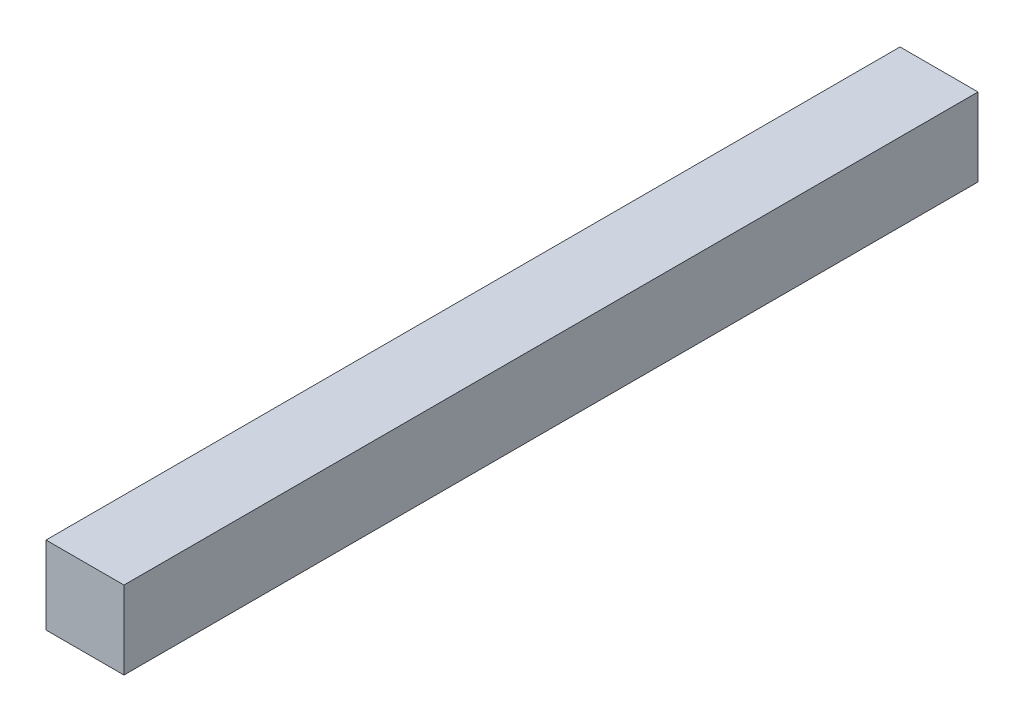
SolidWorks part; units mm, degrees
material "Pine"
ref_plane "Front Plane" through (0, 0, 0) normal (0, 0, 1) x (1, 0, 0)
ref_plane "Top Plane" through (0, 0, 0) normal (0, 1, 0) x (1, 0, 0)
ref_plane "Right Plane" through (0, 0, 0) normal (1, 0, 0) x (0, 0, -1)
sketch "Sketch1" plane through (0, 0, 0) normal (0, 0, 1) x (1, 0, 0)
  line L0 (21, 21) -> (-21, 21)
  line L1 (20, -20) -> (-20, -20)
  line L2 (20, -20) -> (20, 20)
  line L3 (20, 20) -> (-20, 20)
  line L4 (-20, -20) -> (-20, 20)
  line L5 (20, -20) -> (-20, 20) construction
  line L6 (20, 20) -> (-20, -20) construction
  line L7 (-21, -21) -> (-21, 21)
  line L8 (21, -21) -> (-21, -21)
  line L9 (21, -21) -> (21, 21)
  point P0 (0, 0)
  dimension "D1" = 40
  dimension "D2" = 40
  dimension "D3" = 1
extrude "Boss-Extrude1" add sketch "Sketch1" along normal blind 460 contours L8 L9 L0 L7 L1 L4 L3 L2
